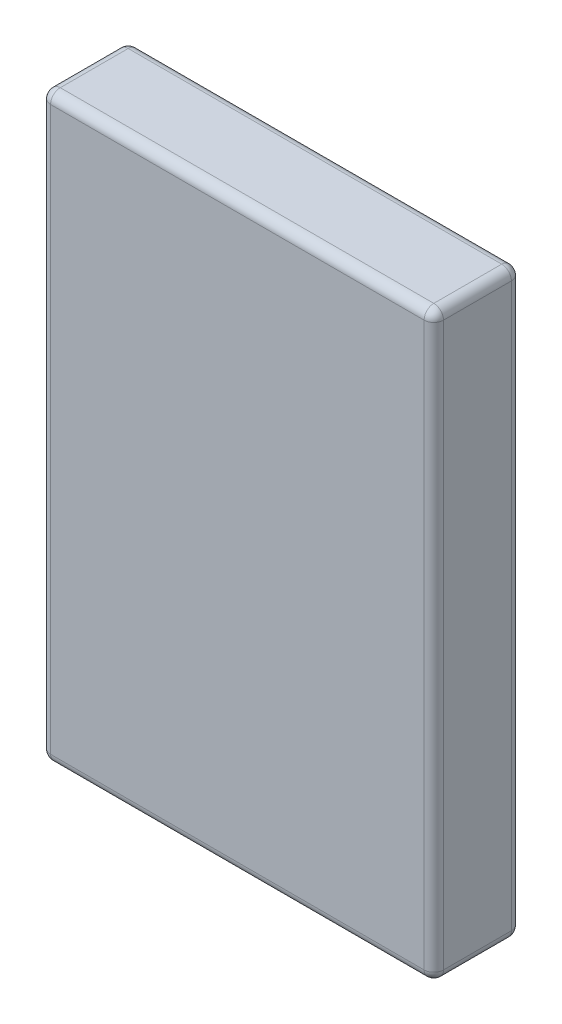
SolidWorks part; units mm, degrees
ref_plane "Front Plane" through (0, 0, 0) normal (0, 0, 1) x (1, 0, 0)
ref_plane "Top Plane" through (0, 0, 0) normal (0, 1, 0) x (1, 0, 0)
ref_plane "Right Plane" through (0, 0, 0) normal (1, 0, 0) x (0, 0, -1)
sketch "Sketch2" plane through (0, 0, 0) normal (0, 1, 0) x (1, 0, 0)
  line L1 (-81, 18) -> (81, 18)
  line L2 (-81, 18) -> (-81, -18)
  line L3 (-81, -18) -> (81, -18)
  line L4 (81, 18) -> (81, -18)
  line L5 (-81, 18) -> (81, -18) construction
  line L6 (-81, -18) -> (81, 18) construction
  point P0 (0, 0)
  dimension "D1" = 162
  dimension "D2" = 36
extrude "Boss-Extrude1" add sketch "Sketch2" along normal blind 240
fillet "Fillet1" radius 4 12 edges at (-81, 120, -18) (-81, 240, 0) (-81, 120, 18) (-81, 0, 0) (81, 0, 0) (0, 0, -18) (0, 0, 18) (81, 240, 0) (81, 120, -18) (81, 120, 18) (0, 240, -18) (0, 240, 18)
